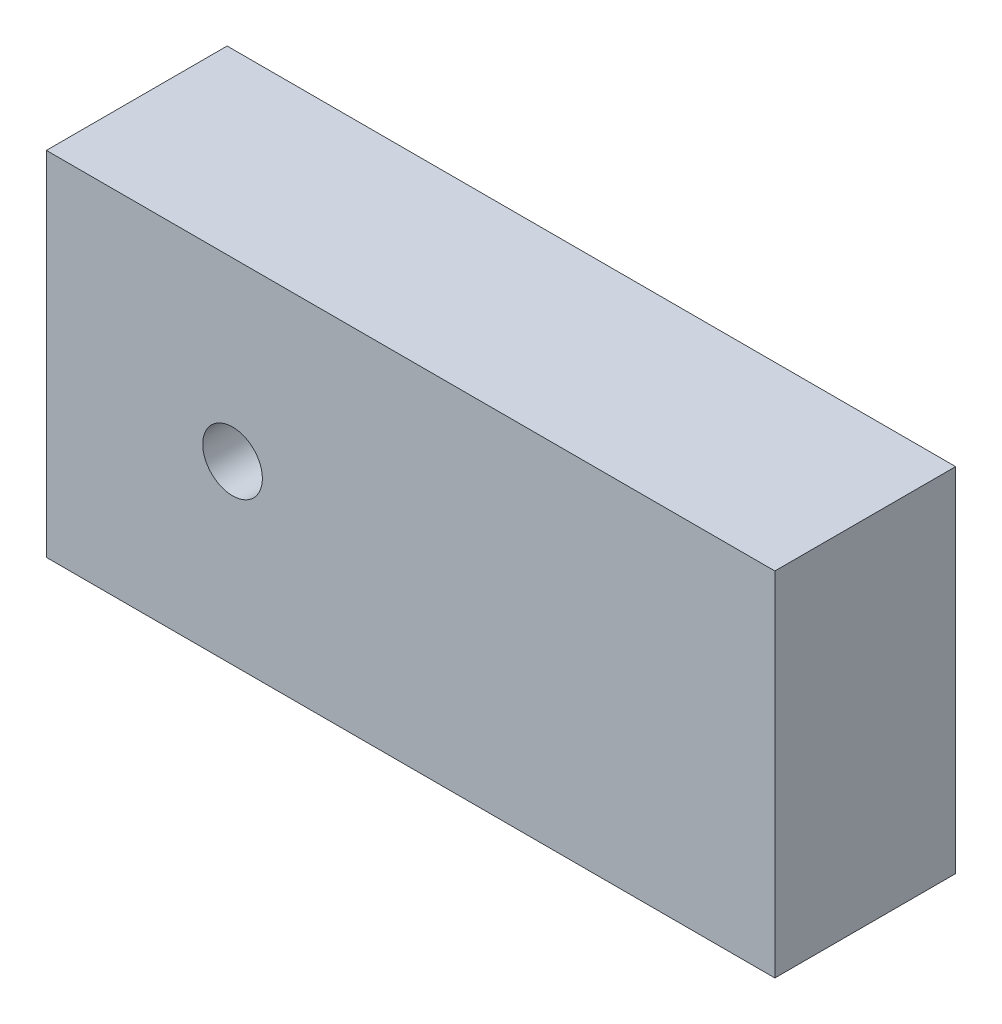
SolidWorks part; units mm, degrees
ref_plane "前视基准面" through (0, 0, 0) normal (0, 0, 1) x (1, 0, 0)
ref_plane "上视基准面" through (0, 0, 0) normal (0, 1, 0) x (1, 0, 0)
ref_plane "右视基准面" through (0, 0, 0) normal (1, 0, 0) x (0, 0, -1)
sketch "草图1" plane through (0, 0, 0) normal (0, 0, 1) x (1, 0, 0)
  line L0 (-29.1307, 0) -> (36.2962, 0) construction
  line L1 (-20.15, -9.75) -> (20.15, -9.75)
  line L2 (-20.15, -9.75) -> (-20.15, 9.75)
  line L3 (-20.15, 9.75) -> (20.15, 9.75)
  line L4 (20.15, -9.75) -> (20.15, 9.75)
  line L5 (-20.15, -9.75) -> (20.15, 9.75) construction
  line L6 (-20.15, 9.75) -> (20.15, -9.75) construction
  line L7 (-9.85, 15.1064) -> (-9.85, -20.9721) construction
  circle A0 centre (-9.85, 0) radius 1.65
  point P0 (0, 0)
  dimension "D1" = 19.5
  dimension "D2" = 40.3
  dimension "D3" = 10.3
extrude "凸台-拉伸1" add sketch "草图1" along normal blind 10
